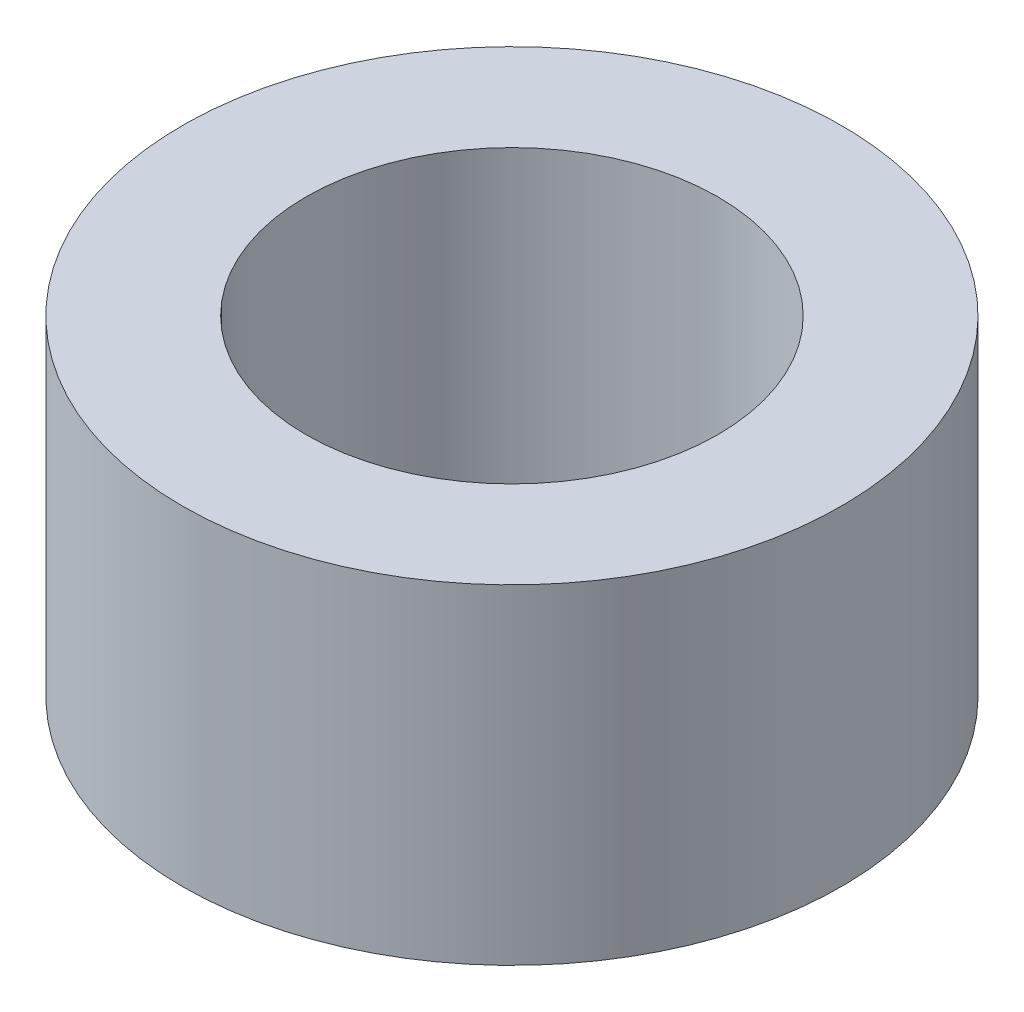
SolidWorks part; units mm, degrees
ref_plane "Front Plane" through (0, 0, 0) normal (0, 0, 1) x (1, 0, 0)
ref_plane "Top Plane" through (0, 0, 0) normal (0, 1, 0) x (1, 0, 0)
ref_plane "Right Plane" through (0, 0, 0) normal (1, 0, 0) x (0, 0, -1)
sketch "Sketch1" plane through (0, 0, 0) normal (0, 1, 0) x (1, 0, 0)
  circle A0 centre (0, 0) radius 5
  circle A1 centre (0, 0) radius 3.125
  dimension "D1" = 10
  dimension "D2" = 6.25
extrude "Boss-Extrude1" add sketch "Sketch1" along normal blind 5
